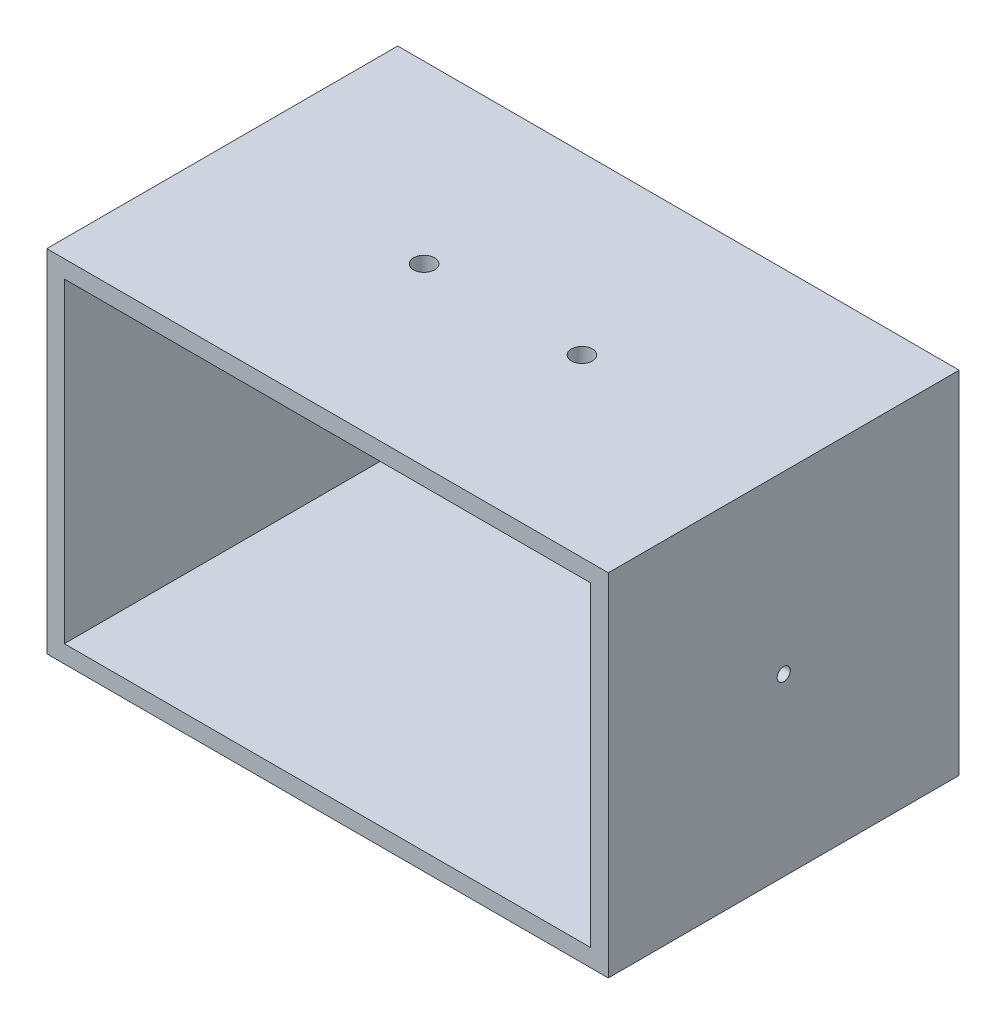
SolidWorks part; units mm, degrees
ref_plane "Front Plane" through (0, 0, 0) normal (0, 0, 1) x (1, 0, 0)
ref_plane "Top Plane" through (0, 0, 0) normal (0, 1, 0) x (1, 0, 0)
ref_plane "Right Plane" through (0, 0, 0) normal (1, 0, 0) x (0, 0, -1)
sketch "Sketch1" plane through (0, 0, 0) normal (0, 1, 0) x (1, 0, 0)
  line L1 (0, 0) -> (203.2, 0)
  line L2 (0, 0) -> (0, 127)
  line L3 (0, 127) -> (203.2, 127)
  line L4 (203.2, 0) -> (203.2, 127)
  dimension "D1" = 127
  dimension "D2" = 203.2
extrude "Boss-Extrude1" add sketch "Sketch1" along normal blind 127
shell "Shell1" thickness 6.35
sketch "Sketch2" plane through (203.2, 0, 0) normal (1, 0, 0) x (0, 0, -1)
  circle A0 centre (63.5, 63.5) radius 2.3813
  dimension "D1" = 4.7625
extrude "Cut-Extrude1" cut sketch "Sketch2" against normal through all
sketch "Sketch4" plane through (0, 127, 0) normal (0, 1, 0) x (1, 0, 0)
  line L0 (76.8316, 63.5) -> (73.0373, 63.5)
  line L1 (126.3684, 63.5) -> (130.1627, 63.5)
  circle A1 centre (73.0373, 63.5) radius 3.7943
  circle A2 centre (130.1627, 63.5) radius 3.7943
  point P0 (0, 0)
extrude "Cut-Extrude3" cut sketch "Sketch4" against normal blind 23.368
